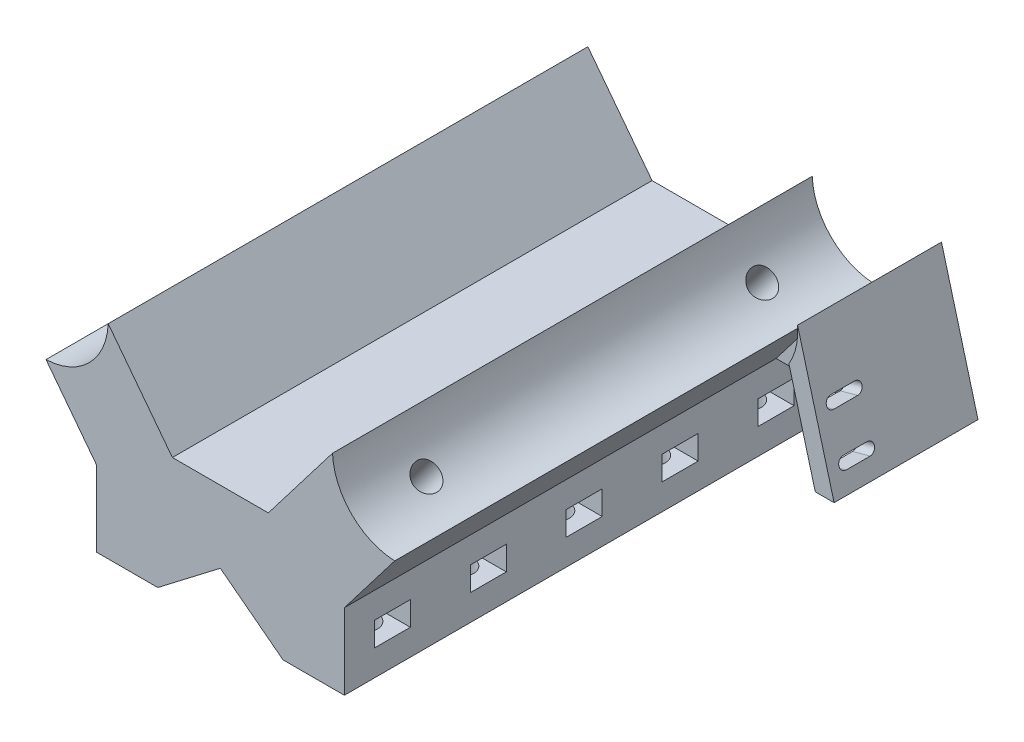
SolidWorks part; units mm, degrees
ref_plane "Alzado" through (0, 0, 0) normal (0, 0, 1) x (1, 0, 0)
ref_plane "Planta" through (0, 0, 0) normal (0, 1, 0) x (1, 0, 0)
ref_plane "Vista lateral" through (0, 0, 0) normal (1, 0, 0) x (0, 0, -1)
sketch "Croquis1" plane through (0, 0, 0) normal (0, 0, 1) x (1, 0, 0)
  line L0 (-25.8547, -27.1886) -> (-25.8547, -43)
  line L2 (-10, -18) -> (10, -18)
  line L3 (-36.3485, -13.4897) -> (-25.8547, -27.1886)
  line L4 (-23.3853, -0.5265) -> (-10, -18)
  line L5 (10, -18) -> (23.3853, -0.5265)
  line L6 (-25.8547, -43) -> (25.8547, -43)
  line L7 (36.3485, -13.4897) -> (25.8547, -27.1886)
  line L9 (25.8547, -27.1886) -> (25.8547, -43)
  arc A0 (-36.3485, -13.4897) -> (-23.3853, -0.5265) centre (-36.875, 0) ccw
  arc A1 (23.3853, -0.5265) -> (36.3485, -13.4897) centre (36.875, 0) ccw
  point P9 (-36.875, 0)
  point P10 (101.07, -110.6752)
  point P15 (0, -141.5754)
  point P17 (0, -141.5754)
  point P18 (96.2884, -112.1371)
  dimension "D1" = 73.75
  dimension "D2" = 27
  dimension "D3" = 27
  dimension "D5" = 26.875
  dimension "D4" = 18
  dimension "D6" = 20
  dimension "D7" = 25
extrude "Saliente-Extruir1" add sketch "Croquis1" along normal blind 100 contours L2 L5 A1 L7 L9 L6 L0 L3 A0 L4
sketch "Croquis3" plane through (0, 0, 100) normal (0, 0, 1) x (1, 0, 0)
  line L2 (0, -33) -> (-29.1594, -55.3371)
  line L3 (0, -33) -> (29.1594, -55.3371)
  line L4 (-25.8547, -43) -> (25.8547, -43) construction
  line L5 (-29.1594, -55.3371) -> (29.1594, -55.3371)
  dimension "D1" = 10
extrude "Cortar-Extruir2" cut sketch "Croquis3" against normal through all
sketch "Croquis4" plane through (15.9308, -20.7965, 0) normal (0.6081, -0.7938, 0) x (-0.7938, -0.6081, 0)
  line L0 (20.0678, -100) -> (36.5121, -100) construction
  line L1 (20.0678, 0) -> (36.5121, 0) construction
  circle A0 centre (28.2899, -85) radius 5
  circle A1 centre (28.2899, -15) radius 5
  dimension "D1" = 10
  dimension "D2" = 15
  dimension "D3" = 10
  dimension "D4" = 15
extrude "Cortar-Extruir3" cut sketch "Croquis4" against normal blind 5
sketch "Croquis5" plane through (12.8902, -16.8272, 0) normal (0.6081, -0.7938, 0) x (-0.7938, -0.6081, 0)
  circle A0 centre (28.2899, -85) radius 2.5
  circle A1 centre (28.2899, -15) radius 2.5
  dimension "D1" = 5
extrude "Cortar-Extruir4" cut sketch "Croquis5" against normal blind 55
sketch "Croquis6" plane through (-15.9308, -20.7965, 0) normal (-0.6081, -0.7938, 0) x (0.7938, -0.6081, 0)
  line L0 (36.5121, 100) -> (20.0678, 100) construction
  line L1 (36.5121, 0) -> (20.0678, 0) construction
  circle A0 centre (28.2899, 85) radius 5
  circle A1 centre (28.2899, 15) radius 5
  dimension "D1" = 15
  dimension "D2" = 10
  dimension "D3" = 15
extrude "Cortar-Extruir5" cut sketch "Croquis6" against normal blind 5
sketch "Croquis7" plane through (-12.8902, -16.8272, 0) normal (-0.6081, -0.7938, 0) x (0.7938, -0.6081, 0)
  circle A0 centre (28.2899, 85) radius 2.75
  circle A1 centre (28.2899, 15) radius 2.75
  dimension "D1" = 5.5
  dimension "D2" = 5.5
extrude "Cortar-Extruir6" cut sketch "Croquis7" against normal blind 55
sketch "Croquis8" plane through (0, -43, 0) normal (0, -1, 0) x (1, 0, 0)
  line L0 (-25.8547, 100) -> (-13.0542, 100) construction
  line L1 (13.0542, 100) -> (25.8547, 100) construction
  circle A0 centre (-20, 90) radius 2.75
  circle A1 centre (20, 90) radius 2.75
  circle A2 centre (20, 70) radius 2.75
  circle A3 centre (-20, 70) radius 2.75
  circle A4 centre (20, 50) radius 2.75
  circle A5 centre (-20, 50) radius 2.75
  circle A6 centre (20, 30) radius 2.75
  circle A7 centre (-20, 30) radius 2.75
  circle A8 centre (20, 10) radius 2.75
  circle A9 centre (-20, 10) radius 2.75
  dimension "D1" = 5.5
  dimension "D2" = 5.5
  dimension "D3" = 10
  dimension "D4" = 10
  dimension "D5" = 40
  dimension "D6" = 20
  dimension "D7" = 5
extrude "Cortar-Extruir7" cut sketch "Croquis8" against normal blind 15
sketch "Croquis9" plane through (25.8547, 0, 0) normal (1, 0, 0) x (0, 0, -1)
  line L0 (-100, -27.1886) -> (-100, -43) construction
  line L1 (-93.75, -37.5943) -> (-86.25, -37.5943)
  line L2 (-93.75, -37.5943) -> (-93.75, -32.5943)
  line L3 (-93.75, -32.5943) -> (-86.25, -32.5943)
  line L4 (-86.25, -37.5943) -> (-86.25, -32.5943)
  line L5 (-93.75, -37.5943) -> (-86.25, -32.5943) construction
  line L6 (-93.75, -32.5943) -> (-86.25, -37.5943) construction
  line L7 (-73.75, -37.5943) -> (-66.25, -37.5943)
  line L8 (-73.75, -32.5943) -> (-66.25, -32.5943)
  line L9 (-73.75, -37.5943) -> (-73.75, -32.5943)
  line L10 (-66.25, -37.5943) -> (-66.25, -32.5943)
  line L11 (-53.75, -37.5943) -> (-46.25, -37.5943)
  line L12 (-53.75, -32.5943) -> (-46.25, -32.5943)
  line L13 (-53.75, -37.5943) -> (-53.75, -32.5943)
  line L14 (-46.25, -37.5943) -> (-46.25, -32.5943)
  line L15 (-33.75, -37.5943) -> (-26.25, -37.5943)
  line L16 (-33.75, -32.5943) -> (-26.25, -32.5943)
  line L17 (-33.75, -37.5943) -> (-33.75, -32.5943)
  line L18 (-26.25, -37.5943) -> (-26.25, -32.5943)
  line L19 (-13.75, -37.5943) -> (-6.25, -37.5943)
  line L20 (-13.75, -32.5943) -> (-6.25, -32.5943)
  line L21 (-13.75, -37.5943) -> (-13.75, -32.5943)
  line L22 (-6.25, -37.5943) -> (-6.25, -32.5943)
  point P0 (-90, -35.0943)
  dimension "D1" = 10
  dimension "D2" = 5
  dimension "D3" = 7.5
  dimension "D4" = 5
extrude "Cortar-Extruir8" cut sketch "Croquis9" against normal blind 12
sketch "Croquis10" plane through (-25.8547, 0, 0) normal (-1, 0, 0) x (0, 0, 1)
  line L0 (100, -27.1886) -> (100, -43) construction
  line L1 (93.75, -32.5943) -> (86.25, -32.5943)
  line L2 (93.75, -32.5943) -> (93.75, -37.5943)
  line L3 (93.75, -37.5943) -> (86.25, -37.5943)
  line L4 (86.25, -32.5943) -> (86.25, -37.5943)
  line L5 (93.75, -32.5943) -> (86.25, -37.5943) construction
  line L6 (93.75, -37.5943) -> (86.25, -32.5943) construction
  line L7 (73.75, -32.5943) -> (73.75, -37.5943)
  line L8 (73.75, -37.5943) -> (66.25, -37.5943)
  line L9 (73.75, -32.5943) -> (66.25, -32.5943)
  line L10 (66.25, -32.5943) -> (66.25, -37.5943)
  line L11 (53.75, -32.5943) -> (53.75, -37.5943)
  line L12 (53.75, -37.5943) -> (46.25, -37.5943)
  line L13 (53.75, -32.5943) -> (46.25, -32.5943)
  line L14 (46.25, -32.5943) -> (46.25, -37.5943)
  line L15 (33.75, -32.5943) -> (33.75, -37.5943)
  line L16 (33.75, -37.5943) -> (26.25, -37.5943)
  line L17 (33.75, -32.5943) -> (26.25, -32.5943)
  line L18 (26.25, -32.5943) -> (26.25, -37.5943)
  line L19 (13.75, -32.5943) -> (13.75, -37.5943)
  line L20 (13.75, -37.5943) -> (6.25, -37.5943)
  line L21 (13.75, -32.5943) -> (6.25, -32.5943)
  line L22 (6.25, -32.5943) -> (6.25, -37.5943)
  point P0 (90, -35.0943)
  dimension "D1" = 10
  dimension "D2" = 7.5
  dimension "D3" = 5
  dimension "D4" = 5
extrude "Cortar-Extruir9" cut sketch "Croquis10" against normal blind 12
sketch "Croquis11" plane through (0, 0, 0) normal (0, 0, -1) x (-1, 0, 0)
  line L1 (-50.3328, 1.0667) -> (-57.9469, -27.1886)
  line L2 (-25.8547, -27.1886) -> (-57.9469, -27.1886)
  line L3 (-25.8547, -27.1886) -> (-36.3485, -13.4897)
  arc A0 (-50.3328, 1.0667) -> (-36.3485, -13.4897) centre (-36.875, 0) ccw
extrude "Saliente-Extruir2" add sketch "Croquis11" against normal blind 10 contours L1 L2 L3 A0
sketch "Croquis12" plane through (0, 0, 10) normal (0, 0, 1) x (1, 0, 0)
  line L0 (54.0261, -27.1886) -> (48.5336, -6.8064)
  line L3 (25.8547, -27.1886) -> (57.9469, -27.1886) construction
  line L4 (54.0261, -27.1886) -> (57.9469, -27.1886)
  line L5 (57.9469, -27.1886) -> (50.3328, 1.0667)
  arc A1 (36.3485, -13.4897) -> (50.3328, 1.0667) centre (36.875, 0) ccw construction
  arc A2 (48.5336, -6.8064) -> (50.3328, 1.0667) centre (36.875, 0) ccw
extrude "Saliente-Extruir3" add sketch "Croquis12" along normal blind 20
sketch "Croquis13" plane through (47.1932, 12.7174, 0) normal (0.9656, 0.2602, 0) x (0, 0, -1)
  line L0 (-26.5, -36.3295) -> (-21.5, -36.3295) construction
  line L1 (-26.5, -35.1295) -> (-21.5, -35.1295)
  line L2 (-26.5, -37.5295) -> (-21.5, -37.5295)
  line L3 (-26.5, -26.3295) -> (-21.5, -26.3295) construction
  line L4 (-26.5, -25.1295) -> (-21.5, -25.1295)
  line L5 (-26.5, -27.5295) -> (-21.5, -27.5295)
  line L9 (-30, -41.3295) -> (0, -41.3295) construction
  line L10 (-30, -41.3295) -> (-30, -12.0663) construction
  arc A0 (-26.5, -35.1295) -> (-26.5, -37.5295) centre (-26.5, -36.3295) ccw
  arc A1 (-21.5, -37.5295) -> (-21.5, -35.1295) centre (-21.5, -36.3295) ccw
  arc A2 (-26.5, -25.1295) -> (-26.5, -27.5295) centre (-26.5, -26.3295) ccw
  arc A3 (-21.5, -27.5295) -> (-21.5, -25.1295) centre (-21.5, -26.3295) ccw
  point P2 (-24, -36.3295)
  point P7 (-24, -26.3295)
  dimension "D2" = 1.2
  dimension "D3" = 1.2
  dimension "D1" = 10
  dimension "D4" = 5
  dimension "D5" = 5
  dimension "D6" = 3.5
extrude "Cortar-Extruir10" cut sketch "Croquis13" against normal blind 10
